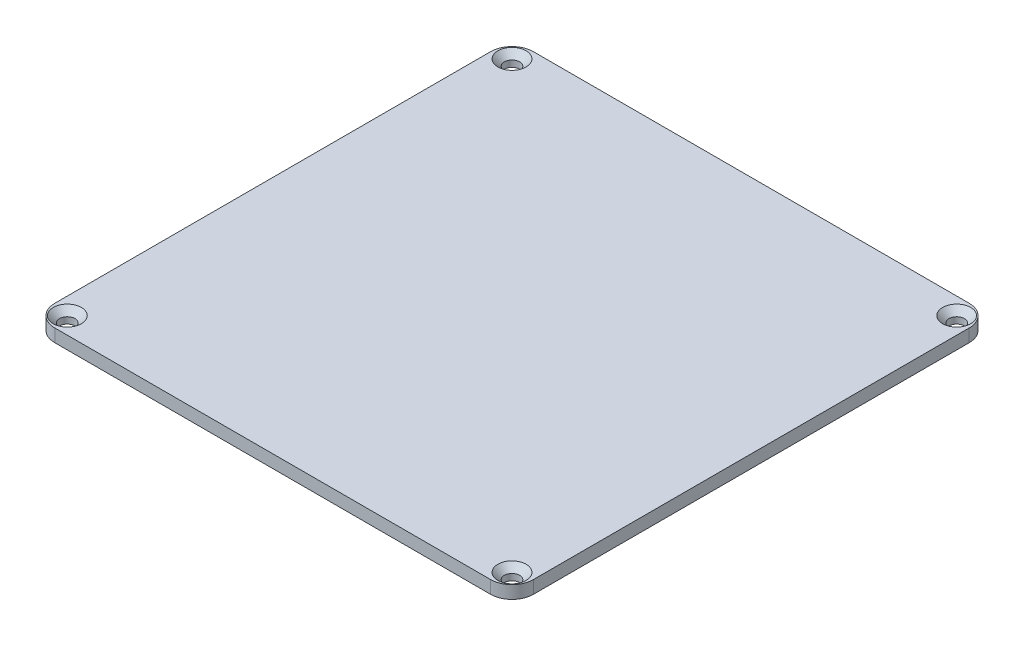
SolidWorks part; units mm, degrees
ref_plane "前视基准面" through (0, 0, 0) normal (0, 0, 1) x (1, 0, 0)
ref_plane "上视基准面" through (0, 0, 0) normal (0, 1, 0) x (1, 0, 0)
ref_plane "右视基准面" through (0, 0, 0) normal (1, 0, 0) x (0, 0, -1)
other "Configuration Table"
sketch "草图1" plane through (0, 0, 0) normal (0, 1, 0) x (1, 0, 0)
  line L1 (-56, 56) -> (56, 56)
  line L2 (-56, 56) -> (-56, -56)
  line L3 (-56, -56) -> (56, -56)
  line L4 (56, 56) -> (56, -56)
  line L5 (-56, 56) -> (56, -56) construction
  line L6 (-56, -56) -> (56, 56) construction
  point P0 (0, 0)
  dimension "D1" = 112
  dimension "D2" = 112
extrude "凸台-拉伸1" add sketch "草图1" along normal blind 3
hole_wizard "M3 十字槽半沉头木螺钉的锥形沉头孔5" positions "草图19" profile "草图20" countersink size "M3" standard "GB" end condition through all
sketch "草图19" plane through (0, 3, 0) normal (0, 1, 0) x (1, 0, 0)
  line L1 (-52.035, 52.035) -> (52.035, 52.035)
  line L3 (-52.035, -52.035) -> (52.035, -52.035)
  point P2 (52.035, -52.035)
  point P97 (-52.035, 52.035)
  point P98 (-52.035, -52.035)
  point P99 (52.035, 52.035)
  dimension "D1" = 104.07
  dimension "D2" = 104.07
sketch "草图20" plane through (52.035, 3, 52.035) normal (1, 0, 0) x (0, 0, 1)
  line L0 (0, 0) -> (0, 3)
  line L1 (0, 3) -> (1.8, 3)
  line L2 (1.8, 3) -> (1.8, 1.5)
  line L3 (1.8, 1.5) -> (3.3, 0)
  line L5 (3.3, 0) -> (0, 0)
  line L6 (-1.8, 1.5) -> (-3.3, 0) construction
  line L11 (0, -6.35) -> (0, 107.95) construction
  dimension "通孔孔直径" = 3.6
  dimension "通孔孔深度" = 3
  dimension "近端锥形沉头孔直径" = 6.6
  dimension "近端锥形沉头孔角度" = 90
fillet "圆角1" radius 5 4 edges at (-56, 1.5, 56) (-56, 1.5, -56) (56, 1.5, -56) (56, 1.5, 56)
